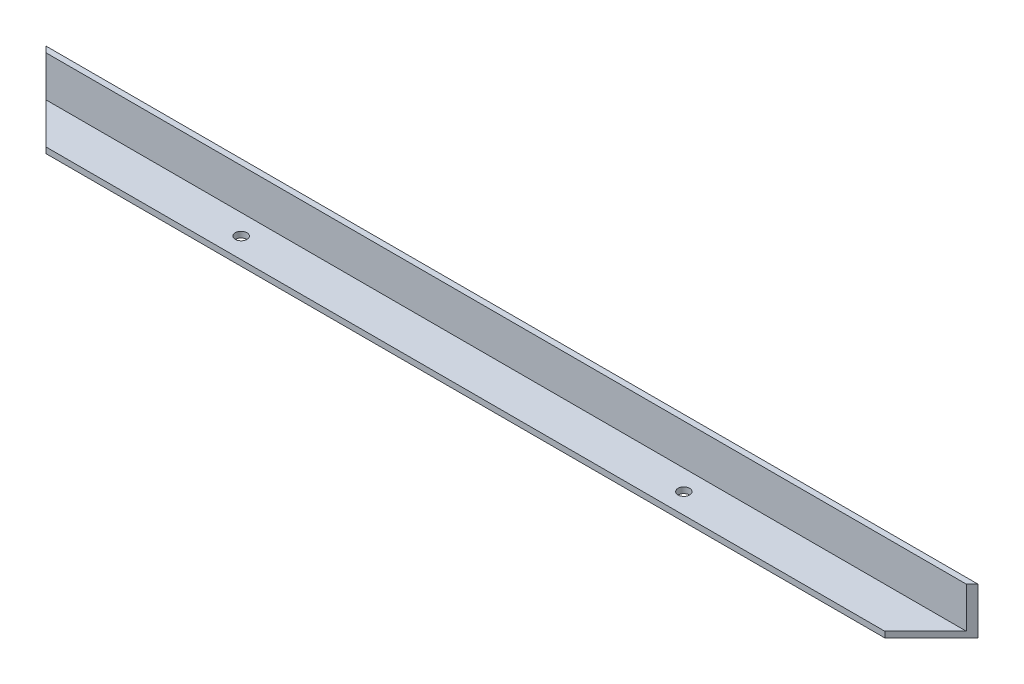
SolidWorks part; units mm, degrees
material "6063-T1"
ref_plane "Front Plane" through (0, 0, 0) normal (0, 0, 1) x (1, 0, 0)
ref_plane "Top Plane" through (0, 0, 0) normal (0, 1, 0) x (1, 0, 0)
ref_plane "Right Plane" through (0, 0, 0) normal (1, 0, 0) x (0, 0, -1)
sketch "Sketch1" plane through (0, 0, 0) normal (0, 1, 0) x (1, 0, 0)
  line L1 (0, 0) -> (-508, 0)
  line L2 (0, 0) -> (0, -25.4)
  line L3 (0, -25.4) -> (-508, -25.4)
  line L4 (-508, 0) -> (-508, -25.4)
  dimension "D1" = 508
  dimension "D2" = 25.4
extrude "Boss-Extrude1" add sketch "Sketch1" along normal blind 3.175
sketch "Sketch2" plane through (0, 3.175, 0) normal (0, 1, 0) x (1, 0, 0)
  line L0 (0, -25.4) -> (0, 0) construction
  line L1 (-508, 0) -> (0, 0)
  line L2 (-508, 0) -> (-508, -3.175)
  line L3 (-508, -3.175) -> (0, -3.175)
  line L4 (0, 0) -> (0, -3.175)
  dimension "D1" = 3.175
extrude "Boss-Extrude2" add sketch "Sketch2" along normal blind 22.225
sketch "Sketch3" plane through (0, 25.4, 0) normal (0, 1, 0) x (1, 0, 0)
  line L0 (0, 0) -> (-52.3316, -52.3316)
  line L1 (-52.3316, -52.3316) -> (49.5361, -29.784)
  line L2 (49.5361, -29.784) -> (0, 0)
  line L3 (0, 0) -> (0.418, 0.0151)
  line L4 (-508, -3.175) -> (0, -3.175) construction
  dimension "D1" = 45
extrude "Cut-Extrude4" cut sketch "Sketch3" against normal up to surface (25.4 mm away) contours L0 L1 L2 up to face at (-254, 0, 12.7)
sketch "Sketch6" plane through (0, 3.175, 0) normal (0, 1, 0) x (1, 0, 0)
  line L0 (-266.7, -25.4) -> (-266.7, -3.175) construction
  line L1 (-508, -25.4) -> (-25.4, -25.4) construction
  line L2 (-508, -3.175) -> (-3.175, -3.175) construction
  circle A0 centre (-146.05, -14.2875) radius 3.175
  circle A1 centre (-387.35, -14.2875) radius 3.175
  dimension "D1" = 6.35
  dimension "D2" = 22.225
  dimension "D3" = 11.1125
  dimension "D4" = 241.3
  dimension "D5" = 120.65
extrude "Cut-Extrude5" cut sketch "Sketch6" against normal up to surface (3.175 mm away) up to face at (-260.35, 0, 12.7)
sketch "Sketch7" plane through (0, 25.4, 0) normal (0, 1, 0) x (1, 0, 0)
  line L0 (-508, 0) -> (-469.6068, -38.3932)
  line L1 (-469.6068, -38.3932) -> (-537.1216, -29.1216)
  line L2 (-537.1216, -29.1216) -> (-508, 0)
  line L3 (0, 0) -> (-508, 0) construction
  dimension "D1" = 45
extrude "Cut-Extrude6" cut sketch "Sketch7" against normal up to surface (25.4 mm away) up to face at (-387.35, 0, 11.1125)
